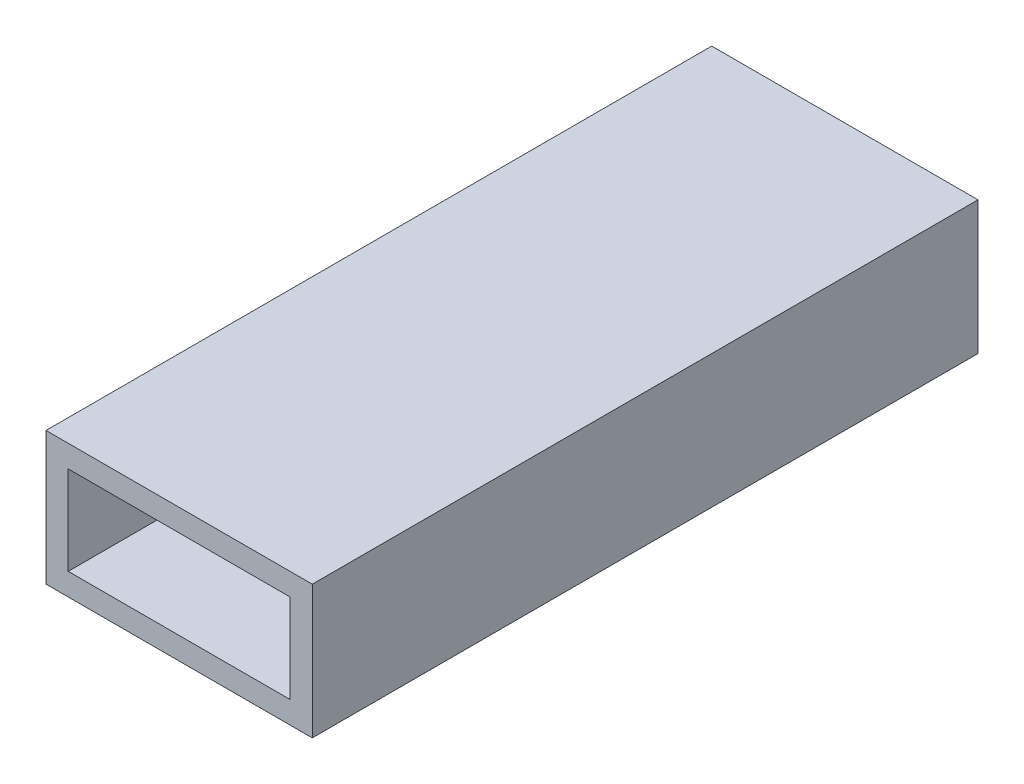
SolidWorks part; units mm, degrees
ref_plane "Plan de face" through (0, 0, 0) normal (0, 0, 1) x (1, 0, 0)
ref_plane "Plan de dessus" through (0, 0, 0) normal (0, 1, 0) x (1, 0, 0)
ref_plane "Plan de droite" through (0, 0, 0) normal (1, 0, 0) x (0, 0, -1)
sketch "Esquisse1" plane through (0, 0, 0) normal (0, 1, 0) x (1, 0, 0)
  line L1 (-30, 75) -> (30, 75)
  line L2 (-30, 75) -> (-30, -75)
  line L3 (-30, -75) -> (30, -75)
  line L4 (30, 75) -> (30, -75)
  dimension "D1" = 60
  dimension "D2" = 30
  dimension "D3" = 150
  dimension "D4" = 75
extrude "Boss.-Extru.1" add sketch "Esquisse1" along normal blind 30
sketch "Esquisse2" plane through (0, 0, 0) normal (0, 0, 1) x (1, 0, 0)
  line L0 (-30, 30) -> (-30, 0) construction
  line L1 (-25, 25) -> (25, 25)
  line L2 (-25, 25) -> (-25, 5)
  line L3 (-25, 5) -> (25, 5)
  line L4 (25, 25) -> (25, 5)
  line L5 (-30, 30) -> (30, 30) construction
  dimension "D1" = 50
  dimension "D2" = 20
  dimension "D3" = 5
  dimension "D4" = 5
extrude "Enlèv. mat.-Extru.1" cut sketch "Esquisse2" against normal blind 70 and the other way blind 75
